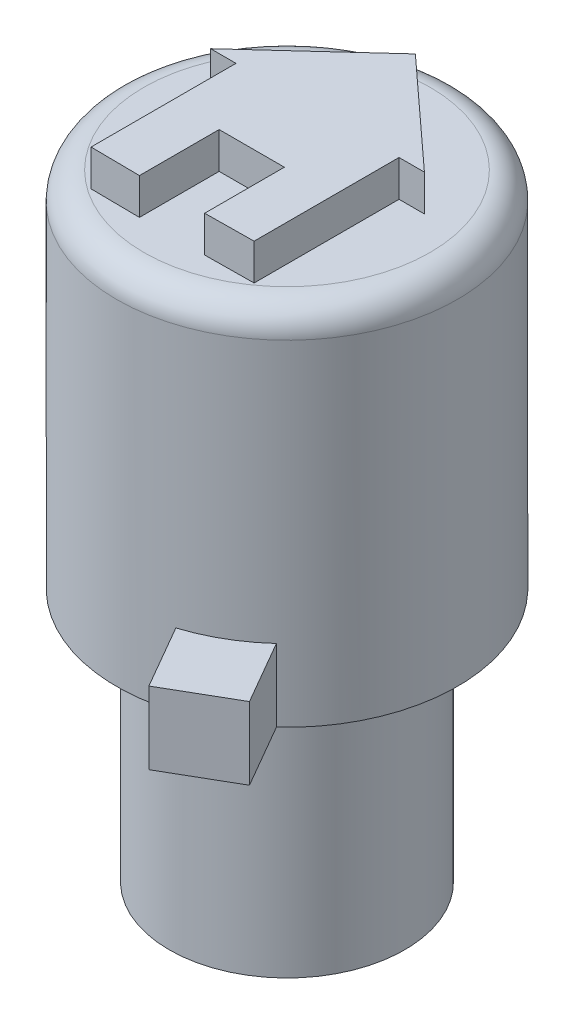
SolidWorks part; units mm, degrees
ref_plane "Front Plane" through (0, 0, 0) normal (0, 0, 1) x (1, 0, 0)
ref_plane "Top Plane" through (0, 0, 0) normal (0, 1, 0) x (1, 0, 0)
ref_plane "Right Plane" through (0, 0, 0) normal (1, 0, 0) x (0, 0, -1)
sketch "Sketch1" plane through (0, 0, 0) normal (0, 1, 0) x (1, 0, 0)
  circle A0 centre (0, 0) radius 3.25
  dimension "D1" = 6.5
extrude "Boss-Extrude1" add sketch "Sketch1" along normal blind 7.018 contours A0
sketch "Sketch2" plane through (0, 0, 0) normal (0, -1, 0) x (1, 0, 0)
  circle A1 centre (0, 0) radius 1.75
  dimension "D1" = 3.5
extrude "Cut-Extrude1" [suppressed] cut sketch "Sketch2" against normal blind 2.5
sketch "Sketch6" plane through (0, 7.018, 0) normal (0, 1, 0) x (1, 0, 0)
  circle A0 centre (0, 0) radius 4.7
  dimension "D1" = 9.4
extrude "Boss-Extrude2" add sketch "Sketch6" along normal blind 10 contours A0
sketch "Sketch7" plane through (0, 17.018, 0) normal (0, 1, 0) x (1, 0, 0)
  line L0 (-2.25, 0) -> (2.25, 0) construction
  line L1 (-2.25, 2.25) -> (2.25, 2.25)
  line L2 (-2.25, 2.25) -> (-2.25, -2.25)
  line L3 (-2.25, -2.25) -> (2.25, -2.25)
  line L4 (2.25, 2.25) -> (2.25, -2.25)
  line L5 (-2.25, 2.25) -> (2.25, -2.25) construction
  line L6 (-2.25, -2.25) -> (2.25, 2.25) construction
  line L7 (-2.25, 2.25) -> (-2.25, -2.25)
  line L8 (0, 0) -> (0, 2.25) construction
  dimension "D1" = 4.5
  dimension "D2" = 4.5
  dimension "D3" = 2.25
sketch "Sketch9" plane through (0, 17.018, 0) normal (0, 1, 0) x (1, 0, 0)
  line L0 (0, 0.8425) -> (0, 3.5425) construction
  line L1 (-2.25, 0.8425) -> (2.25, 0.8425)
  line L2 (-2.25, 0.8425) -> (-2.25, -3.1575)
  line L3 (-2.25, -3.1575) -> (2.25, -3.1575)
  line L4 (2.25, 0.8425) -> (2.25, -3.1575)
  line L7 (-2.95, 0.8425) -> (0, 3.5425)
  line L8 (2.25, 0.8425) -> (2.95, 0.8425)
  line L9 (-2.25, 0.8425) -> (-2.95, 0.8425)
  line L10 (0, 3.5425) -> (2.95, 0.8425)
  line L12 (-0.9, -3.1724) -> (0.9, -3.1724)
  line L13 (-0.9, -3.1724) -> (-0.9, -0.9724)
  line L14 (-0.9, -0.9724) -> (0.9, -0.9724)
  line L15 (0.9, -3.1724) -> (0.9, -0.9724)
  line L19 (0, -0.9724) -> (0, 0.8425) construction
  dimension "D1" = 4
  dimension "D2" = 4.5
  dimension "D3" = 2.7
  dimension "D4" = 0.7
  dimension "D5" = 0.7
  dimension "D6" = 2.2
  dimension "D7" = 1.8
  dimension "D8" = 0.9
  dimension "D12" = 0.8425
  dimension "D13" = 0.9724
sketch "Sketch12" plane through (0, 17.018, 0) normal (0, 1, 0) x (1, 0, 0)
  line L0 (0, 3.5425) -> (-2.95, 0.8425)
  line L1 (-2.95, 0.8425) -> (-2.25, 0.8425)
  line L2 (-2.25, 0.8425) -> (-2.25, -3.1575)
  line L3 (-2.25, -3.1575) -> (-0.9, -3.1724)
  line L4 (-0.9, -3.1724) -> (-0.9, -0.9724)
  line L5 (-0.9, -0.9724) -> (0.9, -0.9724)
  line L6 (0.9, -0.9724) -> (0.9, -3.1724)
  line L7 (0.9, -3.1724) -> (2.25, -3.1575)
  line L8 (2.25, -3.1575) -> (2.25, 0.8425)
  line L9 (2.25, 0.8425) -> (2.95, 0.8425)
  line L10 (2.95, 0.8425) -> (0, 3.5425)
extrude "Boss-Extrude3" add sketch "Sketch12" along normal blind 1
fillet "Fillet1" radius 0.75 1 edges at (0, 17.018, 4.7)
sketch "Sketch13" plane through (0, 7.018, 0) normal (0, -1, 0) x (1, 0, 0)
  line L0 (0, 4.7) -> (0, -4.7) construction
  line L1 (2.35, 4.0703) -> (-2.35, -4.0703) construction
  line L2 (-0.7704, -4.6364) -> (-1.7864, -6.3962)
  line L3 (-1.7864, -6.3962) -> (-4.646, -4.7452)
  line L4 (-4.646, -4.7452) -> (-3.63, -2.9854)
  line L5 (3.1743, 3.4661) -> (4.1903, 5.2258)
  line L6 (4.1903, 5.2258) -> (2.4306, 6.2418)
  line L7 (2.4306, 6.2418) -> (1.4146, 4.4821)
  circle A0 centre (0, 0) radius 4.7 construction
  arc A1 (3.1743, 3.4661) -> (1.4146, 4.4821) centre (0, 0) ccw
  arc A2 (-3.63, -2.9854) -> (-0.7704, -4.6364) centre (0, 0) ccw
  dimension "D1" = 30
  dimension "D2" = 1.651
  dimension "D3" = 2.032
  dimension "D4" = 1.651
  dimension "D5" = 1.016
  dimension "D6" = 1.016
  dimension "D7" = 2.032
extrude "Boss-Extrude4" add sketch "Sketch13" against normal blind 2
